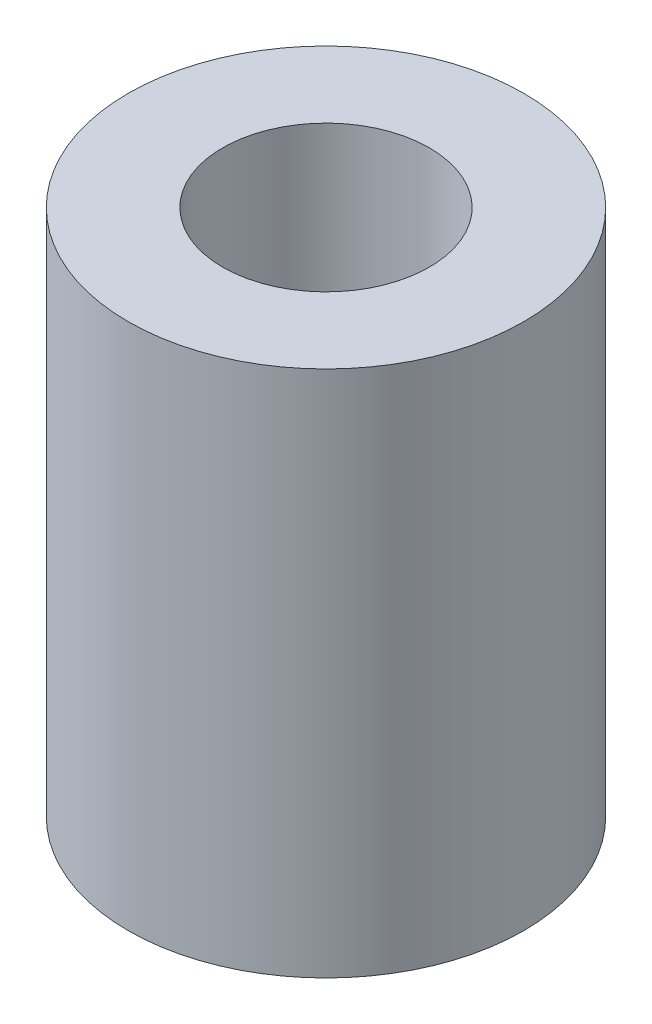
SolidWorks part; units mm, degrees
material "Nylon 101"
ref_plane "Front Plane" through (0, 0, 0) normal (0, 0, 1) x (1, 0, 0)
ref_plane "Top Plane" through (0, 0, 0) normal (0, 1, 0) x (1, 0, 0)
ref_plane "Right Plane" through (0, 0, 0) normal (1, 0, 0) x (0, 0, -1)
sketch "Sketch1" plane through (0, 0, 0) normal (0, 1, 0) x (1, 0, 0)
  circle A0 centre (0, 0) radius 4.7625
  circle A1 centre (0, 0) radius 2.4892
  dimension "D1" = 4.9784
  dimension "D2" = 9.525
extrude "Boss-Extrude1" add sketch "Sketch1" against normal mid plane 12.7
equation "\"Length\"= 0.5"
equation "\"D1@Boss-Extrude1\"=\"Length\""
